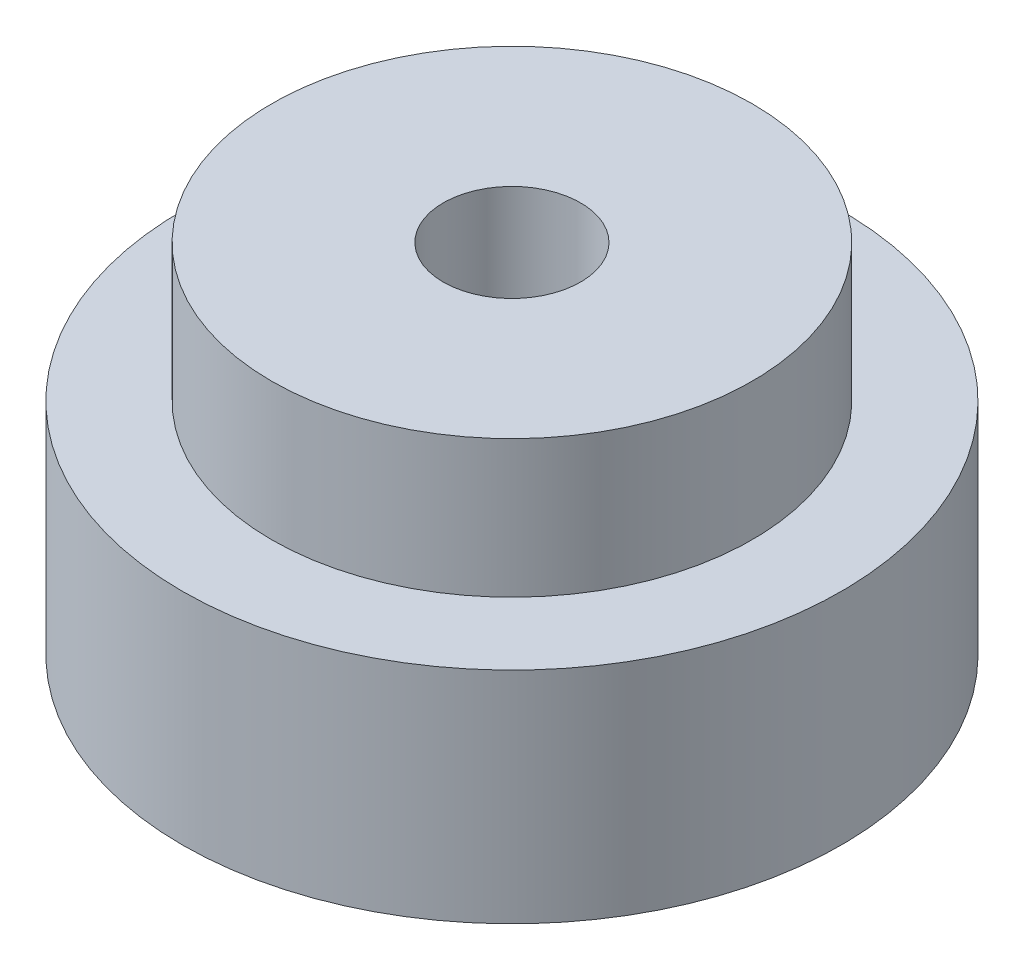
SolidWorks part; units mm, degrees
ref_plane "Front Plane" through (0, 0, 0) normal (0, 0, 1) x (1, 0, 0)
ref_plane "Top Plane" through (0, 0, 0) normal (0, 1, 0) x (1, 0, 0)
ref_plane "Right Plane" through (0, 0, 0) normal (1, 0, 0) x (0, 0, -1)
sketch "Sketch1" plane through (0, 0, 0) normal (0, 1, 0) x (1, 0, 0)
  circle A0 centre (0, 0) radius 24
  dimension "D1" = 48
extrude "Boss-Extrude1" add sketch "Sketch1" along normal blind 16
sketch "Sketch2" plane through (0, 16, 0) normal (0, 1, 0) x (1, 0, 0)
  circle A0 centre (0, 0) radius 17.5
  dimension "D1" = 35
extrude "Boss-Extrude2" add sketch "Sketch2" along normal blind 10
sketch "Sketch3" plane through (0, 26, 0) normal (0, 1, 0) x (1, 0, 0)
  circle A0 centre (0, 0) radius 5
  dimension "D1" = 10
extrude "Cut-Extrude1" cut sketch "Sketch3" against normal blind 26
